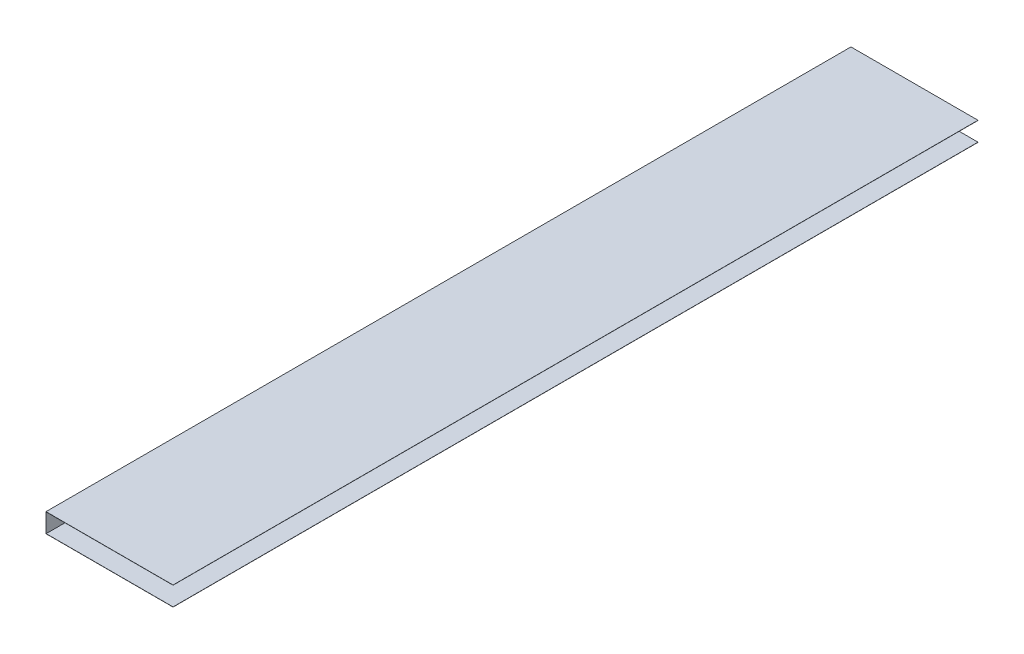
SolidWorks part; units mm, degrees
ref_plane "Front Plane" through (0, 0, 0) normal (0, 0, 1) x (1, 0, 0)
ref_plane "Top Plane" through (0, 0, 0) normal (0, 1, 0) x (1, 0, 0)
ref_plane "Right Plane" through (0, 0, 0) normal (1, 0, 0) x (0, 0, -1)
sketch "Sketch1" plane through (0, 0, 0) normal (0, 0, 1) x (1, 0, 0)
  line L0 (0, 0) -> (146, 0)
  line L1 (146, 0) -> (146, -0.2)
  line L2 (146, -0.2) -> (0.2, -0.2)
  line L3 (0.2, -0.2) -> (0.2, -21.8)
  line L4 (0.2, -21.8) -> (146, -21.8)
  line L5 (146, -21.8) -> (146, -22)
  line L6 (146, -22) -> (0, -22)
  line L7 (0, -22) -> (0, 0)
  point P10 (0, -11)
  dimension "D1" = 0.2
  dimension "D2" = 146
  dimension "D3" = 0.2
  dimension "D4" = 0.2
  dimension "D5" = 22
extrude "Boss-Extrude1" add sketch "Sketch1" along normal blind 925
equation "\"SlotHeight\"= 152mm"
equation "\"WedgeHeight\"= 6mm"
equation "\"PaperHeight\"= \"SlotHeight\" - \"WedgeHeight\""
equation "\"PaperThickness\"= 0.2mm"
equation "\"PaperWidth\"= 22mm"
equation "\"D1@Sketch1\"= \"PaperThickness\""
equation "\"D2@Sketch1\"= \"PaperHeight\""
equation "\"D3@Sketch1\"= \"PaperThickness\""
equation "\"D4@Sketch1\"= \"PaperThickness\""
equation "\"D5@Sketch1\" = \"PaperWidth\""
equation "\"AxialLength\"= 925mm"
equation "\"D1@Boss-Extrude1\"= \"AxialLength\""
